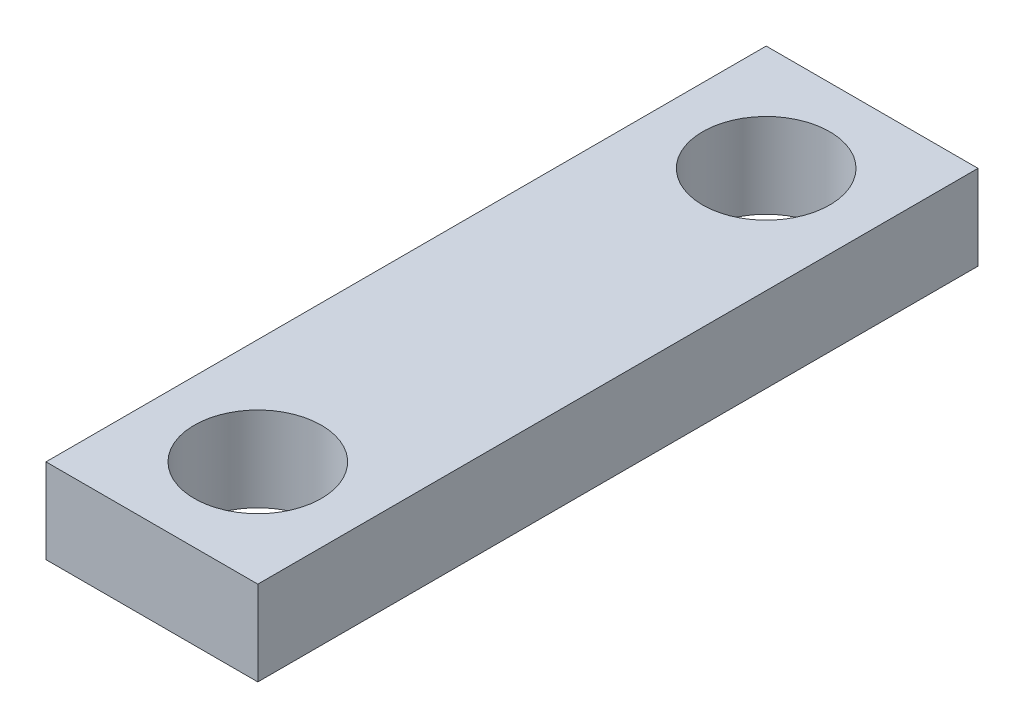
SolidWorks part; units mm, degrees
ref_plane "Front Plane" through (0, 0, 0) normal (0, 0, 1) x (1, 0, 0)
ref_plane "Top Plane" through (0, 0, 0) normal (0, 1, 0) x (1, 0, 0)
ref_plane "Right Plane" through (0, 0, 0) normal (1, 0, 0) x (0, 0, -1)
sketch "Sketch1" plane through (0, 0, 0) normal (0, 1, 0) x (1, 0, 0)
  line L0 (0, 0) -> (6.0313, 0) construction
  line L2 (-3.175, -10.795) -> (3.175, -10.795)
  line L3 (-3.175, -10.795) -> (-3.175, 10.795)
  line L4 (-3.175, 10.795) -> (3.175, 10.795)
  line L5 (3.175, -10.795) -> (3.175, 10.795)
  circle A0 centre (0, 7.62) radius 1.905
  circle A1 centre (0, -7.62) radius 1.905
  point P5 (3.175, 0)
  point P12 (0, 10.795)
  dimension "D1" = 3.81
  dimension "D2" = 7.62
  dimension "D3" = 6.35
  dimension "D4" = 3.175
extrude "Boss-Extrude1" add sketch "Sketch1" along normal blind 2.54
